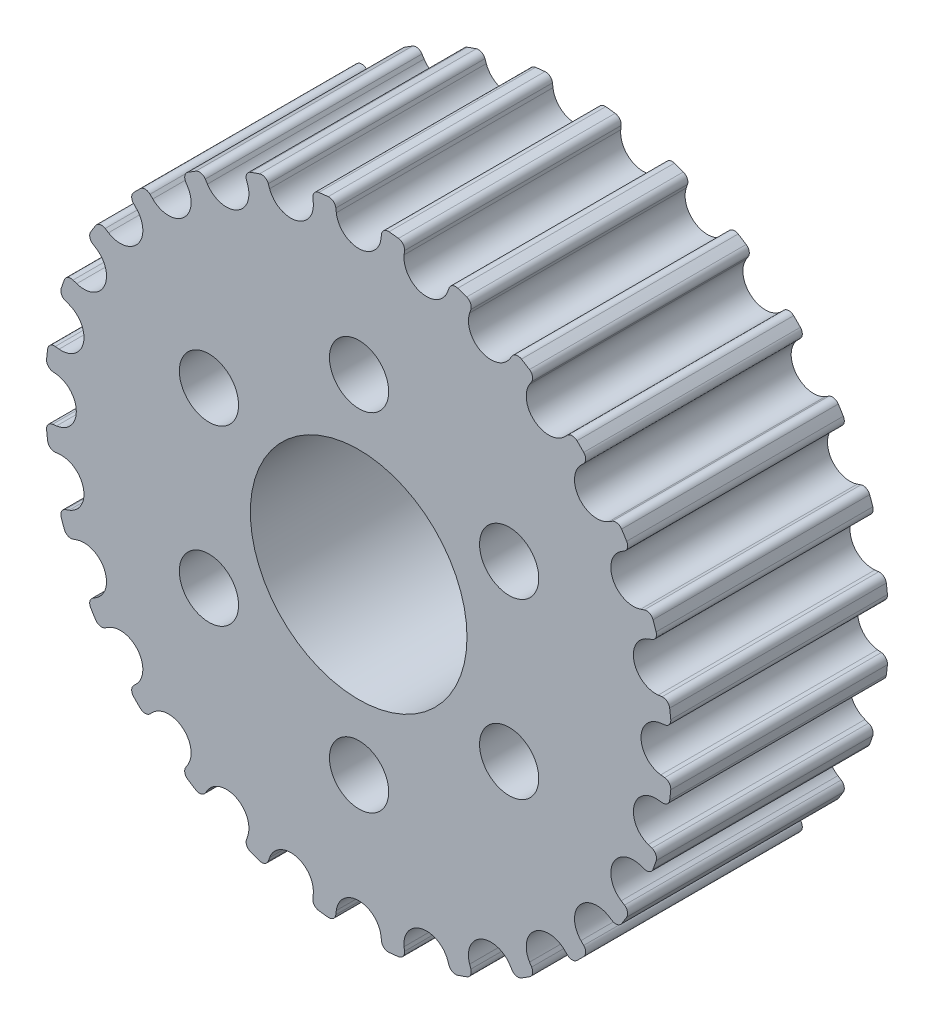
SolidWorks part; units mm, degrees
ref_plane "前视基准面" through (0, 0, 0) normal (0, 0, 1) x (1, 0, 0)
ref_plane "上视基准面" through (0, 0, 0) normal (0, 1, 0) x (1, 0, 0)
ref_plane "右视基准面" through (0, 0, 0) normal (1, 0, 0) x (0, 0, -1)
sketch "草图1" plane through (0, 0, 0) normal (0, 0, 1) x (1, 0, 0)
  line L36 (1.554, 21.1844) -> (1.521, 20.9158)
  line L37 (-1.5757, 20.9158) -> (-1.6087, 21.1844)
  line L38 (-3.2001, 21.0051) -> (-3.1724, 20.7359)
  line L39 (-6.1915, 20.0468) -> (-6.2835, 20.3013)
  line L40 (-7.7951, 19.7724) -> (-7.7082, 19.5161)
  line L41 (-10.4983, 18.1724) -> (-10.6446, 18.4002)
  line L42 (-12.0006, 17.5481) -> (-11.8588, 17.3175)
  line L43 (-14.28, 15.3868) -> (-14.4733, 15.5762)
  line L44 (-15.6057, 14.4438) -> (-15.4162, 14.2505)
  line L45 (-17.347, 11.8294) -> (-17.5776, 11.9711)
  line L46 (-18.4296, 10.6151) -> (-18.2019, 10.4689)
  line L47 (-19.5455, 7.6788) -> (-19.8018, 7.7656)
  line L48 (-20.3308, 6.254) -> (-20.0762, 6.1621)
  line L49 (-20.7653, 3.143) -> (-21.0345, 3.1706)
  line L50 (-21.2138, 1.5792) -> (-20.9452, 1.5463)
  line L51 (-20.9452, -1.5505) -> (-21.2138, -1.5835)
  line L52 (-21.0345, -3.1748) -> (-20.7653, -3.1472)
  line L53 (-20.0762, -6.1663) -> (-20.3308, -6.2583)
  line L54 (-19.8018, -7.7698) -> (-19.5455, -7.683)
  line L55 (-18.2019, -10.4731) -> (-18.4296, -10.6194)
  line L56 (-17.5776, -11.9753) -> (-17.347, -11.8336)
  line L57 (-15.4162, -14.2548) -> (-15.6057, -14.448)
  line L58 (-14.4733, -15.5804) -> (-14.28, -15.391)
  line L59 (-11.8588, -17.3218) -> (-12.0006, -17.5524)
  line L60 (-10.6446, -18.4044) -> (-10.4983, -18.1767)
  line L61 (-7.7082, -19.5203) -> (-7.7951, -19.7766)
  line L62 (-6.2835, -20.3056) -> (-6.1915, -20.051)
  line L63 (-3.1724, -20.7401) -> (-3.2001, -21.0093)
  line L64 (-1.6087, -21.1886) -> (-1.5757, -20.92)
  line L65 (1.521, -20.92) -> (1.554, -21.1886)
  line L66 (3.1454, -21.0093) -> (3.1178, -20.7401)
  line L67 (6.1369, -20.051) -> (6.2288, -20.3056)
  line L68 (7.7404, -19.7766) -> (7.6536, -19.5203)
  line L69 (10.4436, -18.1767) -> (10.5899, -18.4044)
  line L70 (11.9459, -17.5524) -> (11.8042, -17.3218)
  line L71 (14.2253, -15.391) -> (14.4186, -15.5804)
  line L72 (15.551, -14.448) -> (15.3615, -14.2548)
  line L73 (17.2923, -11.8336) -> (17.5229, -11.9753)
  line L74 (18.375, -10.6194) -> (18.1472, -10.4731)
  line L75 (19.4909, -7.683) -> (19.7472, -7.7698)
  line L76 (20.2761, -6.2583) -> (20.0216, -6.1663)
  line L77 (20.7107, -3.1472) -> (20.9799, -3.1748)
  line L78 (21.1592, -1.5835) -> (20.8906, -1.5505)
  line L79 (20.8906, 1.5463) -> (21.1592, 1.5792)
  line L80 (20.9799, 3.1706) -> (20.7107, 3.143)
  line L81 (20.0216, 6.1621) -> (20.2761, 6.254)
  line L82 (19.7472, 7.7656) -> (19.4909, 7.6788)
  line L83 (18.1472, 10.4689) -> (18.375, 10.6151)
  line L84 (17.5229, 11.9711) -> (17.2923, 11.8294)
  line L85 (15.3615, 14.2505) -> (15.551, 14.4438)
  line L86 (14.4186, 15.5762) -> (14.2253, 15.3868)
  line L87 (11.8042, 17.3175) -> (11.9459, 17.5481)
  line L88 (10.5899, 18.4002) -> (10.4436, 18.1724)
  line L89 (7.6536, 19.5161) -> (7.7404, 19.7724)
  line L90 (6.2288, 20.3013) -> (6.1369, 20.0468)
  line L91 (3.1178, 20.7359) -> (3.1454, 21.0051)
  circle A72 centre (0, 0) radius 12 construction
  arc A73 (3.1454, 21.0051) -> (2.7289, 21.5302) centre (2.6679, 21.0541) ccw
  arc A74 (2.7289, 21.5302) -> (2.077, 21.6037) centre (-0.0273, -0.0021) ccw
  arc A75 (2.077, 21.6037) -> (1.554, 21.1844) centre (2.0305, 21.1259) ccw
  arc A76 (-1.5757, 20.9158) -> (1.521, 20.9158) centre (-0.0273, 21.1059) ccw
  arc A77 (-1.6087, 21.1844) -> (-2.1316, 21.6037) centre (-2.0851, 21.1259) ccw
  arc A78 (-2.1316, 21.6037) -> (-2.7835, 21.5302) centre (-0.0273, -0.0021) ccw
  arc A79 (-2.7835, 21.5302) -> (-3.2001, 21.0051) centre (-2.7226, 21.0541) ccw
  arc A80 (-6.1915, 20.0468) -> (-3.1724, 20.7359) centre (-4.7243, 20.5767) ccw
  arc A81 (-6.2835, 20.3013) -> (-6.8866, 20.5937) centre (-6.7349, 20.1383) ccw
  arc A82 (-6.8866, 20.5937) -> (-7.5058, 20.377) centre (-0.0273, -0.0021) ccw
  arc A83 (-7.5058, 20.377) -> (-7.7951, 19.7724) centre (-7.3404, 19.9264) ccw
  arc A84 (-10.4983, 18.1724) -> (-7.7082, 19.5161) centre (-9.1857, 19.0155) ccw
  arc A85 (-10.6446, 18.4002) -> (-11.2976, 18.551) centre (-11.0484, 18.1407) ccw
  arc A86 (-11.2976, 18.551) -> (-11.8531, 18.202) centre (-0.0273, -0.0021) ccw
  arc A87 (-11.8531, 18.202) -> (-12.0006, 17.5481) centre (-11.5916, 17.7994) ccw
  arc A88 (-14.28, 15.3868) -> (-11.8588, 17.3175) centre (-13.1879, 16.5008) ccw
  arc A89 (-14.4733, 15.5762) -> (-15.1435, 15.5779) centre (-14.8093, 15.2334) ccw
  arc A90 (-15.1435, 15.5779) -> (-15.6074, 15.1141) centre (-0.0273, -0.0021) ccw
  arc A91 (-15.6074, 15.1141) -> (-15.6057, 14.4438) centre (-15.2629, 14.7798) ccw
  arc A92 (-17.347, 11.8294) -> (-15.4162, 14.2505) centre (-16.5302, 13.1585) ccw
  arc A93 (-17.5776, 11.9711) -> (-18.2314, 11.8236) centre (-17.8289, 11.5622) ccw
  arc A94 (-18.2314, 11.8236) -> (-18.5804, 11.2682) centre (-0.0273, -0.0021) ccw
  arc A95 (-18.5804, 11.2682) -> (-18.4296, 10.6151) centre (-18.1702, 11.019) ccw
  arc A96 (-19.5455, 7.6788) -> (-18.2019, 10.4689) centre (-19.045, 9.1563) ccw
  arc A97 (-19.8018, 7.7656) -> (-20.4065, 7.4764) centre (-19.9559, 7.311) ccw
  arc A98 (-20.4065, 7.4764) -> (-20.6231, 6.8572) centre (-0.0273, -0.0021) ccw
  arc A99 (-20.6231, 6.8572) -> (-20.3308, 6.254) centre (-20.1677, 6.7055) ccw
  arc A100 (-20.7653, 3.143) -> (-20.0762, 6.1621) centre (-20.6061, 4.6949) ccw
  arc A101 (-21.0345, 3.1706) -> (-21.5596, 2.7541) centre (-21.0835, 2.6931) ccw
  arc A102 (-21.5596, 2.7541) -> (-21.6331, 2.1022) centre (-0.0273, -0.0021) ccw
  arc A103 (-21.6331, 2.1022) -> (-21.2138, 1.5792) centre (-21.1554, 2.0557) ccw
  arc A104 (-20.9452, -1.5505) -> (-20.9452, 1.5463) centre (-21.1353, -0.0021) ccw
  arc A105 (-21.2138, -1.5835) -> (-21.6331, -2.1064) centre (-21.1554, -2.0599) ccw
  arc A106 (-21.6331, -2.1064) -> (-21.5596, -2.7583) centre (-0.0273, -0.0021) ccw
  arc A107 (-21.5596, -2.7583) -> (-21.0345, -3.1748) centre (-21.0835, -2.6974) ccw
  arc A108 (-20.0762, -6.1663) -> (-20.7653, -3.1472) centre (-20.6061, -4.6991) ccw
  arc A109 (-20.3308, -6.2583) -> (-20.6231, -6.8614) centre (-20.1677, -6.7097) ccw
  arc A110 (-20.6231, -6.8614) -> (-20.4065, -7.4806) centre (-0.0273, -0.0021) ccw
  arc A111 (-20.4065, -7.4806) -> (-19.8018, -7.7698) centre (-19.9559, -7.3152) ccw
  arc A112 (-18.2019, -10.4731) -> (-19.5455, -7.683) centre (-19.045, -9.1605) ccw
  arc A113 (-18.4296, -10.6194) -> (-18.5804, -11.2724) centre (-18.1702, -11.0232) ccw
  arc A114 (-18.5804, -11.2724) -> (-18.2314, -11.8279) centre (-0.0273, -0.0021) ccw
  arc A115 (-18.2314, -11.8279) -> (-17.5776, -11.9753) centre (-17.8289, -11.5664) ccw
  arc A116 (-15.4162, -14.2548) -> (-17.347, -11.8336) centre (-16.5302, -13.1627) ccw
  arc A117 (-15.6057, -14.448) -> (-15.6074, -15.1183) centre (-15.2629, -14.7841) ccw
  arc A118 (-15.6074, -15.1183) -> (-15.1435, -15.5822) centre (-0.0273, -0.0021) ccw
  arc A119 (-15.1435, -15.5822) -> (-14.4733, -15.5804) centre (-14.8093, -15.2377) ccw
  arc A120 (-11.8588, -17.3218) -> (-14.28, -15.391) centre (-13.1879, -16.505) ccw
  arc A121 (-12.0006, -17.5524) -> (-11.8531, -18.2062) centre (-11.5916, -17.8037) ccw
  arc A122 (-11.8531, -18.2062) -> (-11.2976, -18.5552) centre (-0.0273, -0.0021) ccw
  arc A123 (-11.2976, -18.5552) -> (-10.6446, -18.4044) centre (-11.0484, -18.145) ccw
  arc A124 (-7.7082, -19.5203) -> (-10.4983, -18.1767) centre (-9.1857, -19.0198) ccw
  arc A125 (-7.7951, -19.7766) -> (-7.5058, -20.3813) centre (-7.3404, -19.9306) ccw
  arc A126 (-7.5058, -20.3813) -> (-6.8866, -20.5979) centre (-0.0273, -0.0021) ccw
  arc A127 (-6.8866, -20.5979) -> (-6.2835, -20.3056) centre (-6.7349, -20.1425) ccw
  arc A128 (-3.1724, -20.7401) -> (-6.1915, -20.051) centre (-4.7243, -20.5809) ccw
  arc A129 (-3.2001, -21.0093) -> (-2.7835, -21.5344) centre (-2.7226, -21.0583) ccw
  arc A130 (-2.7835, -21.5344) -> (-2.1316, -21.6079) centre (-0.0273, -0.0021) ccw
  arc A131 (-2.1316, -21.6079) -> (-1.6087, -21.1886) centre (-2.0851, -21.1301) ccw
  arc A132 (1.521, -20.92) -> (-1.5757, -20.92) centre (-0.0273, -21.1101) ccw
  arc A133 (1.554, -21.1886) -> (2.077, -21.6079) centre (2.0305, -21.1301) ccw
  arc A134 (2.077, -21.6079) -> (2.7289, -21.5344) centre (-0.0273, -0.0021) ccw
  arc A135 (2.7289, -21.5344) -> (3.1454, -21.0093) centre (2.6679, -21.0583) ccw
  arc A136 (6.1369, -20.051) -> (3.1178, -20.7401) centre (4.6696, -20.5809) ccw
  arc A137 (6.2288, -20.3056) -> (6.832, -20.5979) centre (6.6803, -20.1425) ccw
  arc A138 (6.832, -20.5979) -> (7.4512, -20.3813) centre (-0.0273, -0.0021) ccw
  arc A139 (7.4512, -20.3813) -> (7.7404, -19.7766) centre (7.2858, -19.9306) ccw
  arc A140 (10.4436, -18.1767) -> (7.6536, -19.5203) centre (9.1311, -19.0198) ccw
  arc A141 (10.5899, -18.4044) -> (11.243, -18.5552) centre (10.9938, -18.145) ccw
  arc A142 (11.243, -18.5552) -> (11.7984, -18.2062) centre (-0.0273, -0.0021) ccw
  arc A143 (11.7984, -18.2062) -> (11.9459, -17.5524) centre (11.5369, -17.8037) ccw
  arc A144 (14.2253, -15.391) -> (11.8042, -17.3218) centre (13.1333, -16.505) ccw
  arc A145 (14.4186, -15.5804) -> (15.0889, -15.5822) centre (14.7546, -15.2377) ccw
  arc A146 (15.0889, -15.5822) -> (15.5527, -15.1183) centre (-0.0273, -0.0021) ccw
  arc A147 (15.5527, -15.1183) -> (15.551, -14.448) centre (15.2082, -14.7841) ccw
  arc A148 (17.2923, -11.8336) -> (15.3615, -14.2548) centre (16.4756, -13.1627) ccw
  arc A149 (17.5229, -11.9753) -> (18.1768, -11.8279) centre (17.7742, -11.5664) ccw
  arc A150 (18.1768, -11.8279) -> (18.5258, -11.2724) centre (-0.0273, -0.0021) ccw
  arc A151 (18.5258, -11.2724) -> (18.375, -10.6194) centre (18.1155, -11.0232) ccw
  arc A152 (19.4909, -7.683) -> (18.1472, -10.4731) centre (18.9903, -9.1605) ccw
  arc A153 (19.7472, -7.7698) -> (20.3518, -7.4806) centre (19.9012, -7.3152) ccw
  arc A154 (20.3518, -7.4806) -> (20.5685, -6.8614) centre (-0.0273, -0.0021) ccw
  arc A155 (20.5685, -6.8614) -> (20.2761, -6.2583) centre (20.1131, -6.7097) ccw
  arc A156 (20.7107, -3.1472) -> (20.0216, -6.1663) centre (20.5515, -4.6991) ccw
  arc A157 (20.9799, -3.1748) -> (21.505, -2.7583) centre (21.0289, -2.6974) ccw
  arc A158 (21.505, -2.7583) -> (21.5784, -2.1064) centre (-0.0273, -0.0021) ccw
  arc A159 (21.5784, -2.1064) -> (21.1592, -1.5835) centre (21.1007, -2.0599) ccw
  arc A160 (20.8906, 1.5463) -> (20.8906, -1.5505) centre (21.0807, -0.0021) ccw
  arc A161 (21.1592, 1.5792) -> (21.5784, 2.1022) centre (21.1007, 2.0557) ccw
  arc A162 (21.5784, 2.1022) -> (21.505, 2.7541) centre (-0.0273, -0.0021) ccw
  arc A163 (21.505, 2.7541) -> (20.9799, 3.1706) centre (21.0289, 2.6931) ccw
  arc A164 (20.0216, 6.1621) -> (20.7107, 3.143) centre (20.5515, 4.6949) ccw
  arc A165 (20.2761, 6.254) -> (20.5685, 6.8572) centre (20.1131, 6.7055) ccw
  arc A166 (20.5685, 6.8572) -> (20.3518, 7.4764) centre (-0.0273, -0.0021) ccw
  arc A167 (20.3518, 7.4764) -> (19.7472, 7.7656) centre (19.9012, 7.311) ccw
  arc A168 (18.1472, 10.4689) -> (19.4909, 7.6788) centre (18.9903, 9.1563) ccw
  arc A169 (18.375, 10.6151) -> (18.5258, 11.2682) centre (18.1155, 11.019) ccw
  arc A170 (18.5258, 11.2682) -> (18.1768, 11.8236) centre (-0.0273, -0.0021) ccw
  arc A171 (18.1768, 11.8236) -> (17.5229, 11.9711) centre (17.7742, 11.5622) ccw
  arc A172 (15.3615, 14.2505) -> (17.2923, 11.8294) centre (16.4756, 13.1585) ccw
  arc A173 (15.551, 14.4438) -> (15.5527, 15.1141) centre (15.2082, 14.7798) ccw
  arc A174 (15.5527, 15.1141) -> (15.0889, 15.5779) centre (-0.0273, -0.0021) ccw
  arc A175 (15.0889, 15.5779) -> (14.4186, 15.5762) centre (14.7546, 15.2334) ccw
  arc A176 (11.8042, 17.3175) -> (14.2253, 15.3868) centre (13.1333, 16.5008) ccw
  arc A177 (11.9459, 17.5481) -> (11.7984, 18.202) centre (11.5369, 17.7994) ccw
  arc A178 (11.7984, 18.202) -> (11.243, 18.551) centre (-0.0273, -0.0021) ccw
  arc A179 (11.243, 18.551) -> (10.5899, 18.4002) centre (10.9938, 18.1407) ccw
  arc A180 (7.6536, 19.5161) -> (10.4436, 18.1724) centre (9.1311, 19.0155) ccw
  arc A181 (7.7404, 19.7724) -> (7.4512, 20.377) centre (7.2858, 19.9264) ccw
  arc A182 (7.4512, 20.377) -> (6.832, 20.5937) centre (-0.0273, -0.0021) ccw
  arc A183 (6.832, 20.5937) -> (6.2288, 20.3013) centre (6.6803, 20.1383) ccw
  arc A184 (3.1178, 20.7359) -> (6.1369, 20.0468) centre (4.6696, 20.5767) ccw
  circle A185 centre (-0.0273, -0.0021) radius 7.5
  dimension "D1" = 15
extrude "凸台-拉伸1" add sketch "草图1" along normal blind 15
sketch "草图7" plane through (0, 0, 0) normal (0, 0, -1) x (-1, 0, 0)
  circle A0 centre (0, 0) radius 12 construction
  point P3 (0, 12)
  point P6 (10.3923, 6)
  point P7 (10.3923, -6)
  point P8 (0, -12)
  point P9 (-10.3923, -6)
  point P10 (-10.3923, 6)
  point P11 (0, 0)
  dimension "D1" = 24
  dimension "D2" = 6
hole_wizard "Ø4.1 (4.1) 直径孔1" positions "草图8" profile "草图9" hole size "Ø4.1" standard "GB" end condition through all
sketch "草图8" plane through (0, 0, 0) normal (0, 0, -1) x (-1, 0, 0)
  point P0 (0, 12)
  point P3 (10.3923, 6)
  point P6 (10.3923, -6)
  point P9 (0, -12)
  point P12 (-10.3923, -6)
  point P15 (-10.3923, 6)
sketch "草图9" plane through (0, 12, 0) normal (1, 0, 0) x (0, 1, 0)
  line L0 (0, 0) -> (0, 15)
  line L1 (0, 15) -> (2.05, 15)
  line L2 (2.05, 15) -> (2.05, 0)
  line L5 (2.05, 0) -> (0, 0)
  line L11 (0, -6.35) -> (0, 107.95) construction
  dimension "通孔孔直径" = 4.1
  dimension "通孔孔深度" = 15
